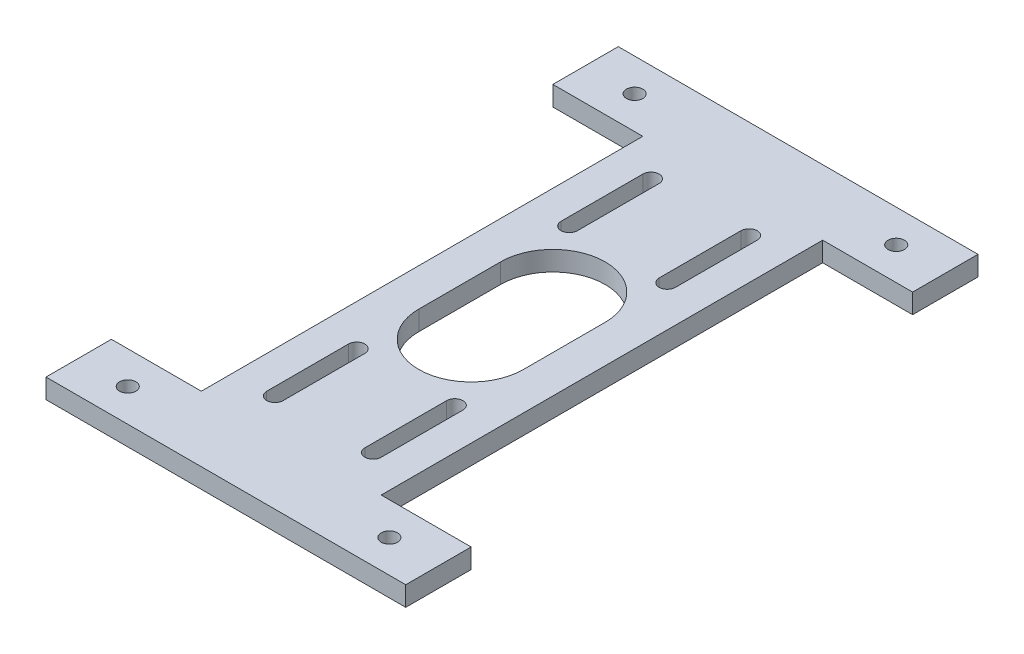
SolidWorks part; units mm, degrees
ref_plane "Front Plane" through (0, 0, 0) normal (0, 0, 1) x (1, 0, 0)
ref_plane "Top Plane" through (0, 0, 0) normal (0, 1, 0) x (1, 0, 0)
ref_plane "Right Plane" through (0, 0, 0) normal (1, 0, 0) x (0, 0, -1)
sketch "Sketch1" plane through (0, 0, 0) normal (0, 1, 0) x (1, 0, 0)
  line L0 (0, -12.5) -> (0, 12.5) construction
  line L1 (-27.5, 67.5) -> (27.5, 67.5)
  line L2 (-27.5, 67.5) -> (-27.5, -67.5)
  line L3 (-27.5, -67.5) -> (27.5, -67.5)
  line L4 (27.5, 67.5) -> (27.5, -67.5)
  line L5 (-27.5, 67.5) -> (27.5, -67.5) construction
  line L6 (-27.5, -67.5) -> (27.5, 67.5) construction
  line L7 (-16, -12.5) -> (-16, 12.5)
  line L8 (16, -12.5) -> (16, 12.5)
  line L9 (-15, -32.5) -> (-15, -57.5) construction
  line L10 (-12.5, -32.5) -> (-12.5, -57.5)
  line L11 (-17.5, -32.5) -> (-17.5, -57.5)
  line L12 (-55, 0) -> (55, 0) construction
  line L13 (-55, -87.5) -> (55, -87.5)
  line L14 (-55, -87.5) -> (-55, -67.5)
  line L15 (-55, -67.5) -> (55, -67.5)
  line L16 (55, -87.5) -> (55, -67.5)
  line L17 (-55, -87.5) -> (55, -67.5) construction
  line L18 (-55, -67.5) -> (55, -87.5) construction
  line L19 (-15, 32.5) -> (-15, 57.5) construction
  line L20 (-12.5, 32.5) -> (-12.5, 57.5)
  line L21 (-17.5, 32.5) -> (-17.5, 57.5)
  line L22 (0, -55) -> (0, 55) construction
  line L23 (15, -32.5) -> (15, -57.5) construction
  line L24 (12.5, -32.5) -> (12.5, -57.5)
  line L25 (17.5, -32.5) -> (17.5, -57.5)
  line L26 (15, 32.5) -> (15, 57.5) construction
  line L27 (12.5, 32.5) -> (12.5, 57.5)
  line L28 (17.5, 32.5) -> (17.5, 57.5)
  line L29 (-55, 67.5) -> (55, 67.5)
  line L30 (55, 87.5) -> (55, 67.5)
  line L31 (-55, 87.5) -> (55, 87.5)
  line L32 (-55, 87.5) -> (-55, 67.5)
  arc A1 (-16, -12.5) -> (16, -12.5) centre (0, -12.5) ccw
  arc A2 (16, 12.5) -> (-16, 12.5) centre (0, 12.5) ccw
  arc A3 (-12.5, -32.5) -> (-17.5, -32.5) centre (-15, -32.5) ccw
  arc A4 (-17.5, -57.5) -> (-12.5, -57.5) centre (-15, -57.5) ccw
  arc A6 (-12.5, 32.5) -> (-17.5, 32.5) centre (-15, 32.5) cw
  arc A7 (-17.5, 57.5) -> (-12.5, 57.5) centre (-15, 57.5) cw
  arc A8 (12.5, -32.5) -> (17.5, -32.5) centre (15, -32.5) cw
  arc A9 (17.5, -57.5) -> (12.5, -57.5) centre (15, -57.5) cw
  arc A10 (12.5, 32.5) -> (17.5, 32.5) centre (15, 32.5) ccw
  arc A11 (17.5, 57.5) -> (12.5, 57.5) centre (15, 57.5) ccw
  circle A12 centre (-40, -77.5) radius 2.5
  circle A13 centre (40, -77.5) radius 2.5
  circle A14 centre (40, 77.5) radius 2.5
  circle A15 centre (-40, 77.5) radius 2.5
  point P0 (0, 0)
  point P2 (0, 87.5)
  point P9 (0, 0)
  point P16 (-15, -45)
  point P21 (0, -77.5)
  point P30 (-15, 45)
  point P39 (15, -45)
  point P46 (15, 45)
  point P57 (-55, -77.5)
  dimension "D1" = 55
  dimension "D3" = 16
  dimension "D5" = 2.5
  dimension "D9" = 5
  dimension "D2" = 135
  dimension "D4" = 25
  dimension "D6" = 20
  dimension "D7" = 45
  dimension "D8" = 15
  dimension "D10" = 40
  dimension "D11" = 110
extrude "Boss-Extrude1" add sketch "Sketch1" along normal blind 6
sketch "Sketch2" plane through (0, 0, 0) normal (0, 1, 0) x (1, 0, 0)
  line L0 (0, -55) -> (0, 55) construction
  line L1 (-55, 0) -> (55, 0) construction
  circle A0 centre (-40, 77.5) radius 6
  circle A1 centre (40, 77.5) radius 6
  circle A2 centre (40, -77.5) radius 6
  circle A3 centre (-40, -77.5) radius 6
  dimension "D1" = 12
